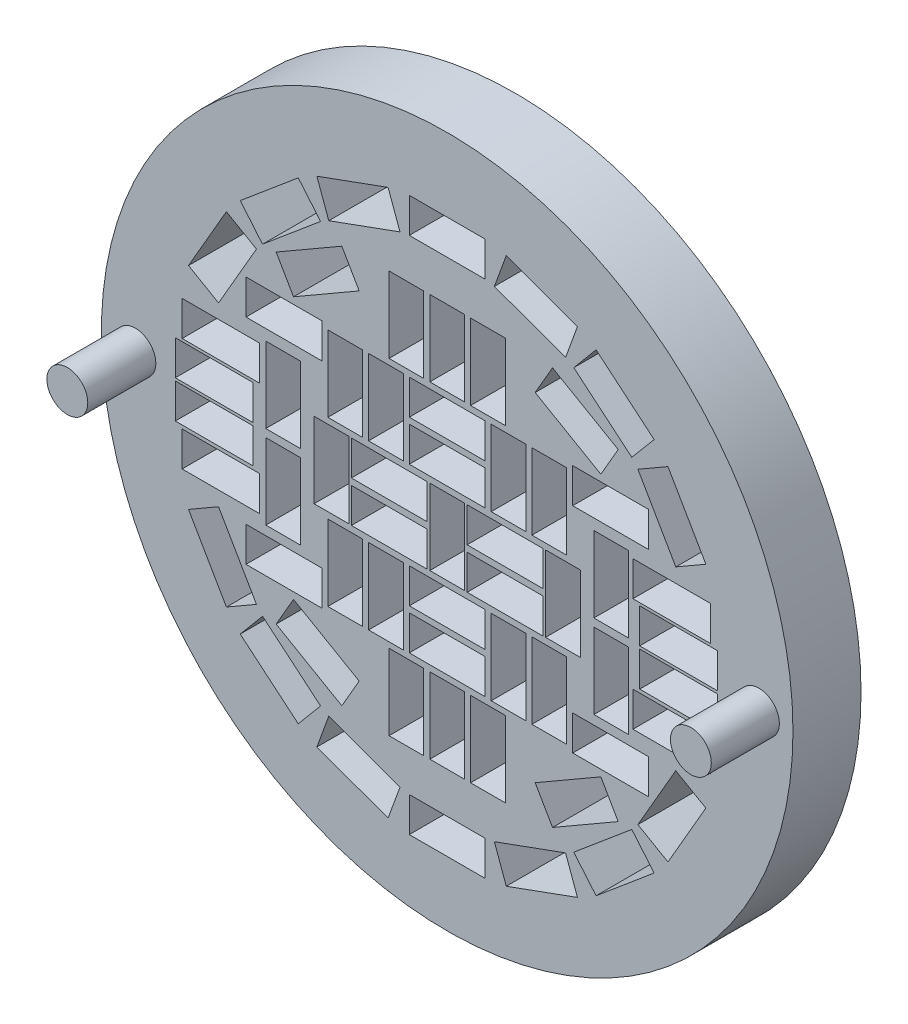
SolidWorks part; units mm, degrees
material "PBT à usage général"
ref_plane "Plan de face" through (0, 0, 0) normal (0, 0, 1) x (1, 0, 0)
ref_plane "Plan de dessus" through (0, 0, 0) normal (0, 1, 0) x (1, 0, 0)
ref_plane "Plan de droite" through (0, 0, 0) normal (1, 0, 0) x (0, 0, -1)
sketch "Esquisse1" plane through (0, 0, 0) normal (0, 0, 1) x (1, 0, 0)
  circle A0 centre (16.6252, 7.1087) radius 25.4
  dimension "D1" = 50.8
extrude "Boss.-Extru.1" add sketch "Esquisse1" along normal blind 5
sketch "Esquisse2" plane through (0, 0, 5) normal (0, 0, 1) x (1, 0, 0)
  line L0 (15.1552, 7.0089) -> (15.1552, 9.5589)
  line L1 (23.8502, 4.0022) -> (23.8502, 9.5672)
  line L2 (15.3502, 4.0022) -> (17.9002, 4.0022)
  line L3 (15.3502, 4.0022) -> (15.3502, 9.5672)
  line L4 (15.3502, 9.5672) -> (17.9002, 9.5672)
  line L5 (17.9002, 4.0022) -> (17.9002, 9.5672)
  line L6 (15.3502, 4.0022) -> (17.9002, 9.5672) construction
  line L7 (15.3502, 9.5672) -> (17.9002, 4.0022) construction
  line L8 (23.8502, 4.0022) -> (26.4002, 4.0022)
  line L9 (26.4002, 4.0022) -> (26.4002, 9.5672)
  line L10 (23.8502, 9.5672) -> (26.4002, 9.5672)
  line L11 (23.8502, 16.0022) -> (23.8502, 21.5672) [skipped]
  line L12 (23.8502, 16.0022) -> (26.4002, 16.0022) [skipped]
  line L13 (26.4002, 16.0022) -> (26.4002, 21.5672) [skipped]
  line L14 (23.8502, 21.5672) -> (26.4002, 21.5672) [skipped]
  line L15 (15.3502, 16.0022) -> (15.3502, 21.5672)
  line L16 (15.3502, 16.0022) -> (17.9002, 16.0022)
  line L17 (17.9002, 16.0022) -> (17.9002, 21.5672)
  line L18 (15.3502, 21.5672) -> (17.9002, 21.5672)
  line L19 (6.8502, 4.0022) -> (6.8502, 9.5672)
  line L20 (6.8502, 4.0022) -> (9.4002, 4.0022)
  line L21 (9.4002, 4.0022) -> (9.4002, 9.5672)
  line L22 (6.8502, 9.5672) -> (9.4002, 9.5672)
  line L23 (6.8502, -7.9978) -> (6.8502, -2.4328) [skipped]
  line L24 (6.8502, -7.9978) -> (9.4002, -7.9978) [skipped]
  line L25 (9.4002, -7.9978) -> (9.4002, -2.4328) [skipped]
  line L26 (6.8502, -2.4328) -> (9.4002, -2.4328) [skipped]
  line L27 (15.3502, -7.9978) -> (15.3502, -2.4328)
  line L28 (15.3502, -7.9978) -> (17.9002, -7.9978)
  line L29 (17.9002, -7.9978) -> (17.9002, -2.4328)
  line L30 (15.3502, -2.4328) -> (17.9002, -2.4328)
  line L31 (23.6552, 7.0089) -> (18.0902, 7.0089)
  line L32 (15.3502, 21.5672) -> (17.9002, 16.0022) construction
  line L33 (23.6552, 7.0089) -> (23.6552, 9.5589)
  line L34 (23.6552, 9.5589) -> (18.0902, 9.5589)
  line L35 (18.0902, 7.0089) -> (18.0902, 9.5589)
  line L36 (23.6552, 7.0089) -> (18.0902, 9.5589) construction
  line L37 (23.6552, 9.5589) -> (18.0902, 7.0089) construction
  line L38 (15.1552, 7.0089) -> (9.5902, 7.0089)
  line L39 (9.5902, 7.0089) -> (9.5902, 9.5589)
  line L40 (15.1552, 9.5589) -> (9.5902, 9.5589)
  line L41 (15.1552, 3.9889) -> (15.1552, 6.5389)
  line L42 (15.1552, 3.9889) -> (9.5902, 3.9889)
  line L43 (9.5902, 3.9889) -> (9.5902, 6.5389)
  line L44 (15.1552, 6.5389) -> (9.5902, 6.5389)
  line L45 (23.6552, 3.9889) -> (23.6552, 6.5389)
  line L46 (23.6552, 3.9889) -> (18.0902, 3.9889)
  line L47 (18.0902, 3.9889) -> (18.0902, 6.5389)
  line L48 (23.6552, 6.5389) -> (18.0902, 6.5389)
  line L49 (16.6252, 6.7847) -> (16.6252, 18.7847) construction
  line L50 (19.4077, 1.0032) -> (19.4077, 3.5532)
  line L51 (19.4077, 10.0102) -> (13.8427, 10.0102)
  line L52 (19.4077, 10.0102) -> (19.4077, 12.5602)
  line L53 (19.4077, 12.5602) -> (13.8427, 12.5602)
  line L54 (13.8427, 10.0102) -> (13.8427, 12.5602)
  line L55 (19.4077, 10.0102) -> (13.8427, 12.5602) construction
  line L56 (19.4077, 12.5602) -> (13.8427, 10.0102) construction
  line L57 (19.4077, 13.0032) -> (13.8427, 13.0032)
  line L58 (19.4077, 13.0032) -> (19.4077, 15.5532)
  line L59 (19.4077, 15.5532) -> (13.8427, 15.5532)
  line L60 (13.8427, 13.0032) -> (13.8427, 15.5532)
  line L61 (19.4077, 13.0032) -> (13.8427, 15.5532) construction
  line L62 (19.4077, 15.5532) -> (13.8427, 13.0032) construction
  line L63 (19.4077, 1.0032) -> (13.8427, 1.0032)
  line L64 (13.8427, 1.0032) -> (13.8427, 3.5532)
  line L65 (19.4077, 3.5532) -> (13.8427, 3.5532)
  line L66 (19.4077, -1.9898) -> (19.4077, 0.5602)
  line L67 (19.4077, -1.9898) -> (13.8427, -1.9898)
  line L68 (13.8427, -1.9898) -> (13.8427, 0.5602)
  line L69 (19.4077, 0.5602) -> (13.8427, 0.5602)
  line L70 (16.6252, 12.7847) -> (12.1247, 12.7847) construction
  line L71 (10.8497, 10.0022) -> (13.3997, 10.0022)
  line L72 (10.8497, 10.0022) -> (10.8497, 15.5672)
  line L73 (10.8497, 15.5672) -> (13.3997, 15.5672)
  line L74 (13.3997, 10.0022) -> (13.3997, 15.5672)
  line L75 (10.8497, 10.0022) -> (13.3997, 15.5672) construction
  line L76 (10.8497, 15.5672) -> (13.3997, 10.0022) construction
  line L77 (7.8597, 10.0022) -> (7.8597, 15.5672)
  line L78 (7.8597, 10.0022) -> (10.4097, 10.0022)
  line L79 (10.4097, 10.0022) -> (10.4097, 15.5672)
  line L80 (7.8597, 15.5672) -> (10.4097, 15.5672)
  line L81 (19.8597, 10.0022) -> (19.8597, 15.5672)
  line L82 (19.8597, 15.5672) -> (22.4097, 15.5672)
  line L83 (22.4097, 10.0022) -> (22.4097, 15.5672)
  line L84 (19.8597, 10.0022) -> (22.4097, 10.0022)
  line L85 (22.8497, 10.0022) -> (22.8497, 15.5672)
  line L86 (22.8497, 10.0022) -> (25.3997, 10.0022)
  line L87 (25.3997, 10.0022) -> (25.3997, 15.5672)
  line L88 (22.8497, 15.5672) -> (25.3997, 15.5672)
  line L89 (19.8597, -2.0278) -> (19.8597, 3.5372)
  line L90 (19.8597, 3.5372) -> (22.4097, 3.5372)
  line L91 (22.4097, -2.0278) -> (22.4097, 3.5372)
  line L92 (19.8597, -2.0278) -> (22.4097, -2.0278)
  line L93 (22.8497, -2.0278) -> (22.8497, 3.5372)
  line L94 (22.8497, -2.0278) -> (25.3997, -2.0278)
  line L95 (25.3997, -2.0278) -> (25.3997, 3.5372)
  line L96 (22.8497, 3.5372) -> (25.3997, 3.5372)
  line L97 (7.8597, -2.0278) -> (7.8597, 3.5372)
  line L98 (7.8597, 3.5372) -> (10.4097, 3.5372)
  line L99 (10.4097, -2.0278) -> (10.4097, 3.5372)
  line L100 (7.8597, -2.0278) -> (10.4097, -2.0278)
  line L101 (10.8497, -2.0278) -> (10.8497, 3.5372)
  line L102 (10.8497, -2.0278) -> (13.3997, -2.0278)
  line L103 (13.3997, -2.0278) -> (13.3997, 3.5372)
  line L104 (10.8497, 3.5372) -> (13.3997, 3.5372)
  line L105 (25.3219, 22.5432) -> (26.194, 24.9394)
  line L106 (19.4077, 24.5672) -> (13.8427, 24.5672)
  line L107 (19.4077, 24.5672) -> (19.4077, 27.1172)
  line L108 (19.4077, 27.1172) -> (13.8427, 27.1172)
  line L109 (13.8427, 24.5672) -> (13.8427, 27.1172)
  line L110 (19.4077, 24.5672) -> (13.8427, 27.1172) construction
  line L111 (19.4077, 27.1172) -> (13.8427, 24.5672) construction
  line L112 (25.3219, 22.5432) -> (20.0925, 24.4465)
  line L113 (20.0925, 24.4465) -> (20.9646, 26.8427)
  line L114 (26.194, 24.9394) -> (20.9646, 26.8427)
  line L115 (30.1871, 18.6184) -> (31.8262, 20.5718)
  line L116 (30.1871, 18.6184) -> (25.9241, 22.1955)
  line L117 (25.9241, 22.1955) -> (27.5632, 24.1489)
  line L118 (31.8262, 20.5718) -> (27.5632, 24.1489)
  line L119 (33.4166, 13.2663) -> (35.6249, 14.5413)
  line L120 (33.4166, 13.2663) -> (30.6341, 18.0857)
  line L121 (30.6341, 18.0857) -> (32.8424, 19.3607)
  line L122 (35.6249, 14.5413) -> (32.8424, 19.3607)
  line L123 (34.6207, 7.1324) -> (37.132, 7.5752) [skipped]
  line L124 (34.6207, 7.1324) -> (33.6544, 12.6129) [skipped]
  line L125 (33.6544, 12.6129) -> (36.1656, 13.0557) [skipped]
  line L126 (37.132, 7.5752) -> (36.1656, 13.0557) [skipped]
  line L127 (33.6544, 0.9566) -> (36.1656, 0.5138) [skipped]
  line L128 (33.6544, 0.9566) -> (34.6207, 6.4371) [skipped]
  line L129 (34.6207, 6.4371) -> (37.132, 5.9943) [skipped]
  line L130 (36.1656, 0.5138) -> (37.132, 5.9943) [skipped]
  line L131 (30.6341, -4.5162) -> (32.8424, -5.7912)
  line L132 (30.6341, -4.5162) -> (33.4166, 0.3032)
  line L133 (33.4166, 0.3032) -> (35.6249, -0.9718)
  line L134 (32.8424, -5.7912) -> (35.6249, -0.9718)
  line L135 (25.9241, -8.626) -> (27.5632, -10.5794)
  line L136 (25.9241, -8.626) -> (30.1871, -5.0489)
  line L137 (30.1871, -5.0489) -> (31.8262, -7.0023)
  line L138 (27.5632, -10.5794) -> (31.8262, -7.0023)
  line L139 (20.0925, -10.877) -> (20.9646, -13.2732)
  line L140 (20.0925, -10.877) -> (25.3219, -8.9737)
  line L141 (25.3219, -8.9737) -> (26.194, -11.3699)
  line L142 (20.9646, -13.2732) -> (26.194, -11.3699)
  line L143 (13.8427, -10.9978) -> (13.8427, -13.5478)
  line L144 (13.8427, -10.9978) -> (19.4077, -10.9978)
  line L145 (19.4077, -10.9978) -> (19.4077, -13.5478)
  line L146 (13.8427, -13.5478) -> (19.4077, -13.5478)
  line L147 (7.9285, -8.9737) -> (7.0564, -11.3699)
  line L148 (7.9285, -8.9737) -> (13.1579, -10.877)
  line L149 (13.1579, -10.877) -> (12.2858, -13.2732)
  line L150 (7.0564, -11.3699) -> (12.2858, -13.2732)
  line L151 (3.0633, -5.0489) -> (1.4242, -7.0023)
  line L152 (3.0633, -5.0489) -> (7.3264, -8.626)
  line L153 (7.3264, -8.626) -> (5.6872, -10.5794)
  line L154 (1.4242, -7.0023) -> (5.6872, -10.5794)
  line L155 (-0.1661, 0.3032) -> (-2.3745, -0.9718)
  line L156 (-0.1661, 0.3032) -> (2.6164, -4.5162)
  line L157 (2.6164, -4.5162) -> (0.408, -5.7912)
  line L158 (-2.3745, -0.9718) -> (0.408, -5.7912)
  line L159 (-1.3703, 6.4371) -> (-3.8816, 5.9943) [skipped]
  line L160 (-1.3703, 6.4371) -> (-0.404, 0.9566) [skipped]
  line L161 (-0.404, 0.9566) -> (-2.9152, 0.5138) [skipped]
  line L162 (-3.8816, 5.9943) -> (-2.9152, 0.5138) [skipped]
  line L163 (-0.404, 12.6129) -> (-2.9152, 13.0557) [skipped]
  line L164 (-0.404, 12.6129) -> (-1.3703, 7.1324) [skipped]
  line L165 (-1.3703, 7.1324) -> (-3.8816, 7.5752) [skipped]
  line L166 (-2.9152, 13.0557) -> (-3.8816, 7.5752) [skipped]
  line L167 (2.6164, 18.0857) -> (0.408, 19.3607)
  line L168 (2.6164, 18.0857) -> (-0.1661, 13.2663)
  line L169 (-0.1661, 13.2663) -> (-2.3745, 14.5413)
  line L170 (0.408, 19.3607) -> (-2.3745, 14.5413)
  line L171 (7.3264, 22.1955) -> (5.6872, 24.1489)
  line L172 (7.3264, 22.1955) -> (3.0633, 18.6184)
  line L173 (3.0633, 18.6184) -> (1.4242, 20.5718)
  line L174 (5.6872, 24.1489) -> (1.4242, 20.5718)
  line L179 (14.9032, 21.5612) -> (14.9032, 15.9962)
  line L180 (20.8932, 21.5612) -> (18.3432, 21.5612)
  line L181 (20.8932, 21.5612) -> (20.8932, 15.9962)
  line L182 (20.8932, 15.9962) -> (18.3432, 15.9962)
  line L183 (18.3432, 21.5612) -> (18.3432, 15.9962)
  line L184 (20.8932, 21.5612) -> (18.3432, 15.9962) construction
  line L185 (20.8932, 15.9962) -> (18.3432, 21.5612) construction
  line L186 (14.9032, 21.5612) -> (12.3532, 21.5612)
  line L187 (12.3532, 21.5612) -> (12.3532, 15.9962)
  line L188 (14.9032, 15.9962) -> (12.3532, 15.9962)
  line L189 (14.9032, -2.4388) -> (14.9032, -8.0038)
  line L190 (14.9032, -2.4388) -> (12.3532, -2.4388)
  line L191 (12.3532, -2.4388) -> (12.3532, -8.0038)
  line L192 (14.9032, -8.0038) -> (12.3532, -8.0038)
  line L193 (20.8932, -2.4388) -> (20.8932, -8.0038)
  line L194 (20.8932, -2.4388) -> (18.3432, -2.4388)
  line L195 (18.3432, -2.4388) -> (18.3432, -8.0038)
  line L196 (20.8932, -8.0038) -> (18.3432, -8.0038)
  line L197 (5.8502, 7.0089) -> (5.8502, 12.5739)
  line L198 (29.9502, 7.0089) -> (27.4002, 7.0089)
  line L199 (29.9502, 7.0089) -> (29.9502, 12.5739)
  line L200 (29.9502, 12.5739) -> (27.4002, 12.5739)
  line L201 (27.4002, 7.0089) -> (27.4002, 12.5739)
  line L202 (29.9502, 7.0089) -> (27.4002, 12.5739) construction
  line L203 (29.9502, 12.5739) -> (27.4002, 7.0089) construction
  line L204 (5.8502, 7.0089) -> (3.3002, 7.0089)
  line L205 (3.3002, 7.0089) -> (3.3002, 12.5739)
  line L206 (5.8502, 12.5739) -> (3.3002, 12.5739)
  line L207 (5.8502, 0.8689) -> (5.8502, 6.4339)
  line L208 (5.8502, 0.8689) -> (3.3002, 0.8689)
  line L209 (3.3002, 0.8689) -> (3.3002, 6.4339)
  line L210 (5.8502, 6.4339) -> (3.3002, 6.4339)
  line L211 (29.9502, 0.8689) -> (29.9502, 6.4339)
  line L212 (29.9502, 0.8689) -> (27.4002, 0.8689)
  line L213 (27.4002, 0.8689) -> (27.4002, 6.4339)
  line L214 (29.9502, 6.4339) -> (27.4002, 6.4339)
  line L219 (13.1579, 24.4465) -> (12.2858, 26.8427)
  line L220 (13.1579, 24.4465) -> (7.9285, 22.5432)
  line L221 (7.9285, 22.5432) -> (7.0564, 24.9394)
  line L222 (12.2858, 26.8427) -> (7.0564, 24.9394)
  point P0 (16.6252, 18.7847)
  point P1 (16.6252, 18.7847)
  point P2 (20.8727, 8.2839)
  point P5 (16.6252, 6.7847)
  point P50 (16.6252, 11.2852)
  point P55 (16.6252, 14.2782)
  point P60 (12.1247, 12.7847)
  point P75 (16.6252, 25.8422)
  point P76 (9.1347, 12.7847)
  point P109 (19.6182, 18.7787)
  point P180 (16.6252, 6.7847)
  point P183 (28.6752, 9.7914)
  dimension "D1" = 5.565
  dimension "D2" = 2.55
  dimension "D7" = 12
  dimension "D8" = 0.19
  dimension "D11" = 0.443
  dimension "D12" = 0.443
  dimension "D14" = 2
  dimension "D15" = 0.443
  dimension "D18" = 3
  dimension "D20" = 0.443
  dimension "D21" = 0.443
  dimension "D24" = 1
  dimension "D3" = 2
  dimension "D4" = 2
  dimension "D5" = 2
  dimension "D6" = 2
  dimension "D9" = 2
  dimension "D10" = 2
  dimension "D13" = 2
  dimension "D16" = 2
  dimension "D17" = 2
  dimension "D22" = 2
  dimension "D23" = 2
  dimension "D25" = 2
  dimension "D26" = 2
  dimension "D19" = 18
extrude "Enlèv. mat.-Extru.1" cut sketch "Esquisse2" against normal through all
sketch "Esquisse3" plane through (0, 0, 5) normal (0, 0, 1) x (1, 0, 0)
  line L0 (3.3002, 12.5739) -> (3.3002, 7.0089) construction
  line L1 (2.8572, 9.6672) -> (-2.8428, 9.6672)
  line L2 (2.8572, 9.6672) -> (2.8572, 12.2172)
  line L3 (2.8572, 12.2172) -> (-2.8428, 12.2172)
  line L4 (-2.8428, 9.6672) -> (-2.8428, 12.2172)
  line L5 (2.8572, 9.6672) -> (-2.8428, 12.2172) construction
  line L6 (2.8572, 12.2172) -> (-2.8428, 9.6672) construction
  line L7 (9.4002, 9.5672) -> (6.8502, 9.5672) construction
  line L8 (35.9672, 9.6672) -> (35.9672, 12.2172)
  line L9 (35.9672, 9.6672) -> (30.2672, 9.6672)
  line L10 (30.2672, 9.6672) -> (30.2672, 12.2172)
  line L11 (35.9672, 12.2172) -> (30.2672, 12.2172)
  line L12 (35.9672, 1.3672) -> (35.9672, 3.9172)
  line L13 (35.9672, 1.3672) -> (30.2672, 1.3672)
  line L14 (30.2672, 1.3672) -> (30.2672, 3.9172)
  line L15 (35.9672, 3.9172) -> (30.2672, 3.9172)
  line L16 (2.8572, 1.3672) -> (2.8572, 3.9172)
  line L17 (2.8572, 1.3672) -> (-2.8428, 1.3672)
  line L18 (-2.8428, 1.3672) -> (-2.8428, 3.9172)
  line L19 (2.8572, 3.9172) -> (-2.8428, 3.9172)
  line L20 (36.4672, 6.9172) -> (36.4672, 9.4672)
  line L21 (2.3572, 6.9172) -> (-3.3428, 6.9172)
  line L22 (2.3572, 6.9172) -> (2.3572, 9.4672)
  line L23 (2.3572, 9.4672) -> (-3.3428, 9.4672)
  line L24 (-3.3428, 6.9172) -> (-3.3428, 9.4672)
  line L25 (2.3572, 6.9172) -> (-3.3428, 9.4672) construction
  line L26 (2.3572, 9.4672) -> (-3.3428, 6.9172) construction
  line L27 (36.4672, 6.9172) -> (30.7672, 6.9172)
  line L28 (30.7672, 6.9172) -> (30.7672, 9.4672)
  line L29 (36.4672, 9.4672) -> (30.7672, 9.4672)
  line L30 (36.4672, 4.1672) -> (36.4672, 6.7172)
  line L31 (36.4672, 4.1672) -> (30.7672, 4.1672)
  line L32 (30.7672, 4.1672) -> (30.7672, 6.7172)
  line L33 (36.4672, 6.7172) -> (30.7672, 6.7172)
  line L34 (2.3572, 4.1672) -> (2.3572, 6.7172)
  line L35 (2.3572, 4.1672) -> (-3.3428, 4.1672)
  line L36 (-3.3428, 4.1672) -> (-3.3428, 6.7172)
  line L37 (2.3572, 6.7172) -> (-3.3428, 6.7172)
  point P0 (0.0072, 10.9422)
  point P9 (-0.4928, 8.1922)
  point P26 (2.3572, 8.1922)
  dimension "D1" = 5.7
  dimension "D2" = 2.55
  dimension "D3" = 0.443
  dimension "D4" = 0.1
  dimension "D7" = 0.2
  dimension "D8" = 0.5
  dimension "D5" = 2
  dimension "D6" = 2
  dimension "D9" = 2
  dimension "D10" = 2
extrude "Enlèv. mat.-Extru.2" cut sketch "Esquisse3" against normal through all
sketch "Esquisse4" plane through (0, 0, 5) normal (0, 0, 1) x (1, 0, 0)
  line L0 (25.8467, 13.3739) -> (25.8467, 15.9239)
  line L1 (1.8467, 13.3739) -> (7.4167, 13.3739)
  line L2 (1.8467, 13.3739) -> (1.8467, 15.9239)
  line L3 (1.8467, 15.9239) -> (7.4167, 15.9239)
  line L4 (7.4167, 13.3739) -> (7.4167, 15.9239)
  line L5 (1.8467, 13.3739) -> (7.4167, 15.9239) construction
  line L6 (1.8467, 15.9239) -> (7.4167, 13.3739) construction
  line L7 (7.8597, 15.5672) -> (7.8597, 10.0022) construction
  line L8 (5.8502, 12.5739) -> (3.3002, 12.5739) construction
  line L9 (25.8467, 13.3739) -> (31.4167, 13.3739)
  line L10 (31.4167, 13.3739) -> (31.4167, 15.9239)
  line L11 (25.8467, 15.9239) -> (31.4167, 15.9239)
  line L12 (25.8467, -2.3561) -> (25.8467, 0.1939)
  line L13 (25.8467, -2.3561) -> (31.4167, -2.3561)
  line L14 (31.4167, -2.3561) -> (31.4167, 0.1939)
  line L15 (25.8467, 0.1939) -> (31.4167, 0.1939)
  line L16 (1.8467, -2.3561) -> (1.8467, 0.1939)
  line L17 (1.8467, -2.3561) -> (7.4167, -2.3561)
  line L18 (7.4167, -2.3561) -> (7.4167, 0.1939)
  line L19 (1.8467, 0.1939) -> (7.4167, 0.1939)
  line L28 (-8.7748, 7.1087) -> (16.6252, 7.1087) construction
  line L29 (3.0633, 18.6184) -> (5.2533, 18.6184) construction
  line L30 (4.0633, 18.6184) -> (8.8871, 21.4034)
  line L31 (8.8871, 21.4034) -> (28.776, 21.4034) construction
  line L32 (8.8871, 21.4034) -> (10.1621, 19.195)
  line L33 (10.1621, 19.195) -> (5.3383, 16.41)
  line L34 (5.3383, 16.41) -> (4.0633, 18.6184)
  line L35 (10.1621, 19.195) -> (30.3285, 19.195) construction
  line L36 (5.3383, 16.41) -> (30.3285, 16.41) construction
  line L37 (4.0633, 18.6184) -> (31.15, 18.6184) construction
  line L38 (29.1871, 18.6184) -> (24.3633, 21.4034)
  line L39 (29.1871, 18.6184) -> (27.9121, 16.41)
  line L40 (27.9121, 16.41) -> (23.0883, 19.195)
  line L41 (23.0883, 19.195) -> (24.3633, 21.4034)
  line L42 (5.3383, 16.41) -> (5.3383, -8.2495) construction
  line L43 (4.0633, 18.6184) -> (4.0633, -5.0489) construction
  line L44 (10.1621, 19.195) -> (10.1621, -10.5655) construction
  line L45 (8.8871, 21.4034) -> (8.8871, -10.5655) construction
  line L46 (4.0633, -5.0489) -> (8.8871, -7.8339)
  line L47 (4.0633, -5.0489) -> (5.3383, -2.8405)
  line L48 (5.3383, -2.8405) -> (10.1621, -5.6255)
  line L49 (10.1621, -5.6255) -> (8.8871, -7.8339)
  line L50 (4.0633, -5.0489) -> (29.1871, -5.0489) construction
  line L51 (10.1621, -5.6255) -> (28.776, -5.6255) construction
  line L52 (5.3383, -2.8405) -> (30.9686, -2.8405) construction
  line L53 (8.8871, -7.8339) -> (28.297, -7.8339) construction
  line L54 (29.1871, -5.0489) -> (24.3633, -7.8339)
  line L55 (29.1871, -5.0489) -> (27.9121, -2.8405)
  line L56 (27.9121, -2.8405) -> (23.0883, -5.6255)
  line L57 (23.0883, -5.6255) -> (24.3633, -7.8339)
  circle A0 centre (16.6252, 7.1087) radius 25.4 construction
  point P0 (4.6317, 14.6489)
  dimension "D1" = 5.57
  dimension "D2" = 2.55
  dimension "D3" = 0.443
  dimension "D4" = 0.8
  dimension "D7" = 5.57
  dimension "D8" = 2.55
  dimension "D9" = 1
  dimension "D10" = 1
  dimension "D11" = 5.57
  dimension "D12" = 0
  dimension "D13" = 1
  dimension "D14" = 2.55
  dimension "D5" = 2
  dimension "D6" = 2
extrude "Enlèv. mat.-Extru.3" cut sketch "Esquisse4" against normal through all
sketch "Esquisse5" plane through (0, 0, 5) normal (0, 0, 1) x (1, 0, 0)
  line L0 (-8.7748, 7.1087) -> (42.0252, 7.1087) construction
  circle A0 centre (16.6252, 7.1087) radius 25.4 construction
  circle A1 centre (-6.2748, 7.1087) radius 1.5
  circle A2 centre (39.5252, 7.1087) radius 1.5
  point P12 (16.6252, 7.1087)
  dimension "D1" = 3
  dimension "D3" = 2
  dimension "D2" = 2.5
extrude "Boss.-Extru.2" add sketch "Esquisse5" along normal blind 5
